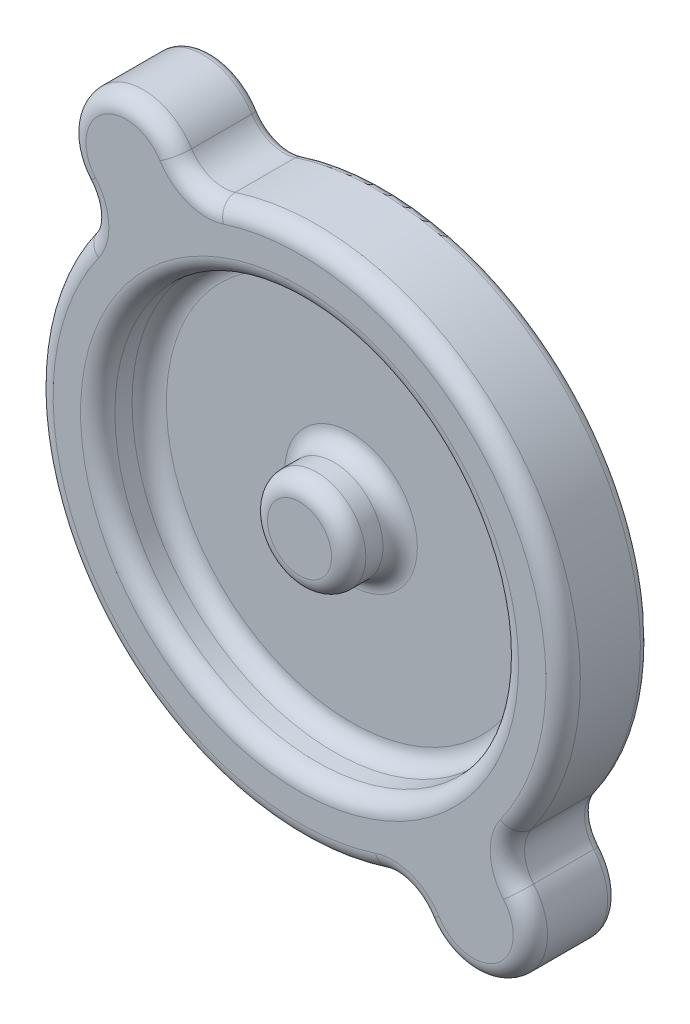
SolidWorks part; units mm, degrees
ref_plane "Front Plane" through (0, 0, 0) normal (0, 0, 1) x (1, 0, 0)
ref_plane "Top Plane" through (0, 0, 0) normal (0, 1, 0) x (1, 0, 0)
ref_plane "Right Plane" through (0, 0, 0) normal (1, 0, 0) x (0, 0, -1)
sketch "Sketch2" plane through (0, 0, 0) normal (0, 0, 1) x (1, 0, 0)
  arc A0 (-9.248, 19.7268) -> (-6.0205, 18.5473) centre (-6.881, 21.1983) ccw
  arc A1 (-9.248, 19.7268) -> (-16.05, 14.7334) centre (-12.8419, 17.4928) ccw
  arc A2 (-15.8916, 11.3007) -> (-16.05, 14.7334) centre (-18.163, 12.9159) ccw
  arc A3 (-15.8916, 11.3007) -> (6.0205, -18.5473) centre (0, 0) ccw
  arc A4 (9.248, -19.7268) -> (6.0205, -18.5473) centre (6.881, -21.1983) ccw
  arc A5 (9.248, -19.7268) -> (16.05, -14.7334) centre (12.8419, -17.4928) ccw
  arc A6 (15.8916, -11.3007) -> (16.05, -14.7334) centre (18.163, -12.9159) ccw
  arc A7 (15.8916, -11.3007) -> (-6.0205, 18.5473) centre (0, 0) ccw
extrude "Extrude1" add sketch "Sketch2" along normal blind 6.35
sketch "Sketch3" plane through (0, 0, 6.35) normal (0, 0, 1) x (1, 0, 0)
  circle A0 centre (0, 0) radius 3.634
  circle A1 centre (0, 0) radius 14.9316
extrude "Extrude2" cut sketch "Sketch3" against normal blind 3.81
fillet "Fillet1" radius 1.27 4 edges at (14.9316, 0, 6.35) (14.9316, 0, 2.54) (3.634, 0, 6.35) (3.634, 0, 2.54)
fillet "Fillet2" radius 1.27 8 edges at (-7.8377, 18.5805, 6.35) (15.719, 11.5397, 6.35) (15.3788, -13.0444, 6.35) (15.346, -20.9039, 6.35) (7.8377, -18.5805, 6.35) (-15.719, -11.5397, 6.35) (-15.3788, 13.0444, 6.35) (-15.346, 20.9039, 6.35)
fillet "Fillet3" radius 0.635 8 edges at (-15.3788, 13.0444, 0) (-15.719, -11.5397, 0) (7.8377, -18.5805, 0) (15.346, -20.9039, 0) (15.3788, -13.0444, 0) (15.719, 11.5397, 0) (-7.8377, 18.5805, 0) (-15.346, 20.9039, 0)
scale "Scale1" scale about origin uniform scaling yes scale factor 1.1
